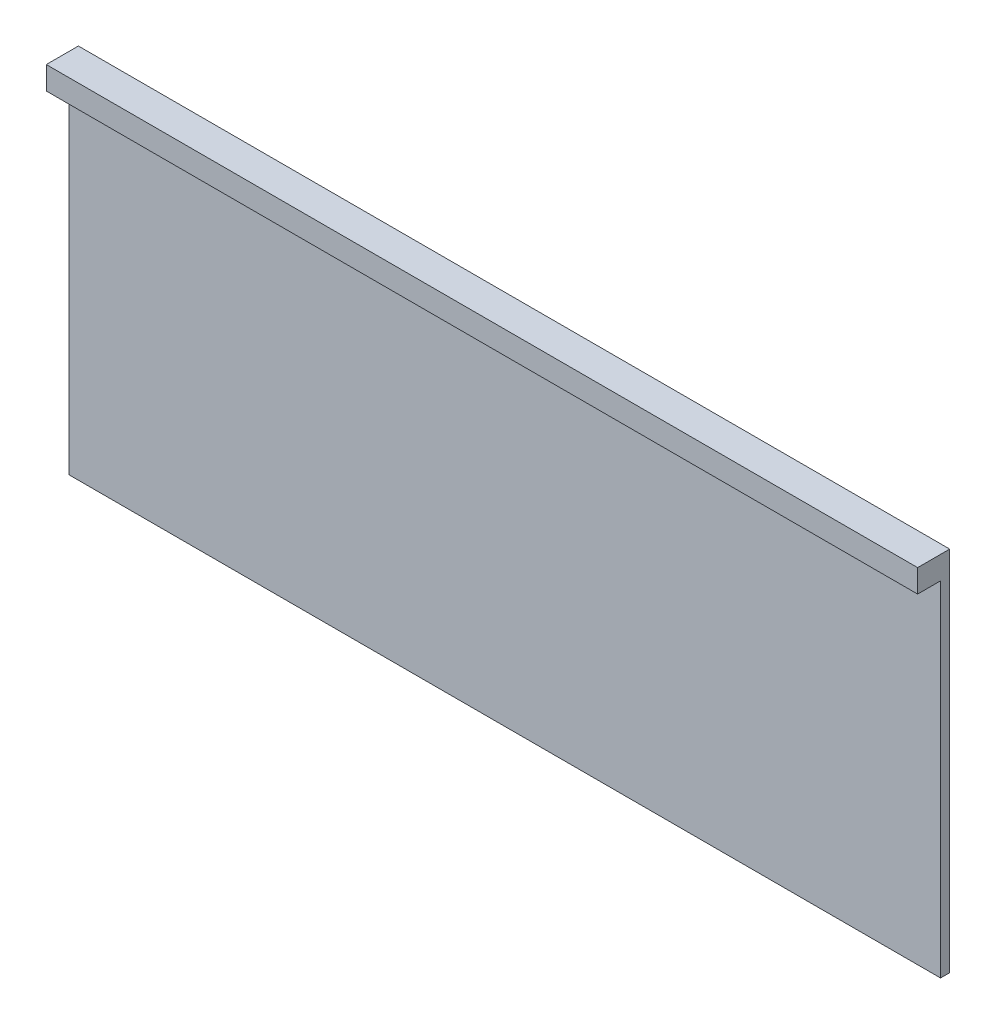
SolidWorks part; units mm, degrees
ref_plane "Alzado" through (0, 0, 0) normal (0, 0, 1) x (1, 0, 0)
ref_plane "Planta" through (0, 0, 0) normal (0, 1, 0) x (1, 0, 0)
ref_plane "Vista lateral" through (0, 0, 0) normal (1, 0, 0) x (0, 0, -1)
sketch "Croquis1" plane through (0, 0, 0) normal (0, 0, 1) x (1, 0, 0)
  line L1 (-76, 30) -> (0, 30)
  line L2 (-76, 30) -> (-76, -2)
  line L3 (-76, -2) -> (0, -2)
  line L4 (0, 30) -> (0, -2)
  dimension "D1" = 76
  dimension "D2" = 32
  dimension "D6" = 0
  dimension "D8" = 30
extrude "Saliente-Extruir1" add sketch "Croquis1" along normal blind 0.8
sketch "Croquis3" plane through (0, 0, 0.8) normal (0, 0, 1) x (1, 0, 0)
  line L0 (0, -2) -> (0, 30) construction
  line L1 (-76, 30) -> (0, 30)
  line L2 (-76, 30) -> (-76, 28)
  line L3 (-76, 28) -> (0, 28)
  line L4 (0, 30) -> (0, 28)
  dimension "D1" = 2
extrude "Saliente-Extruir2" add sketch "Croquis3" along normal blind 2
